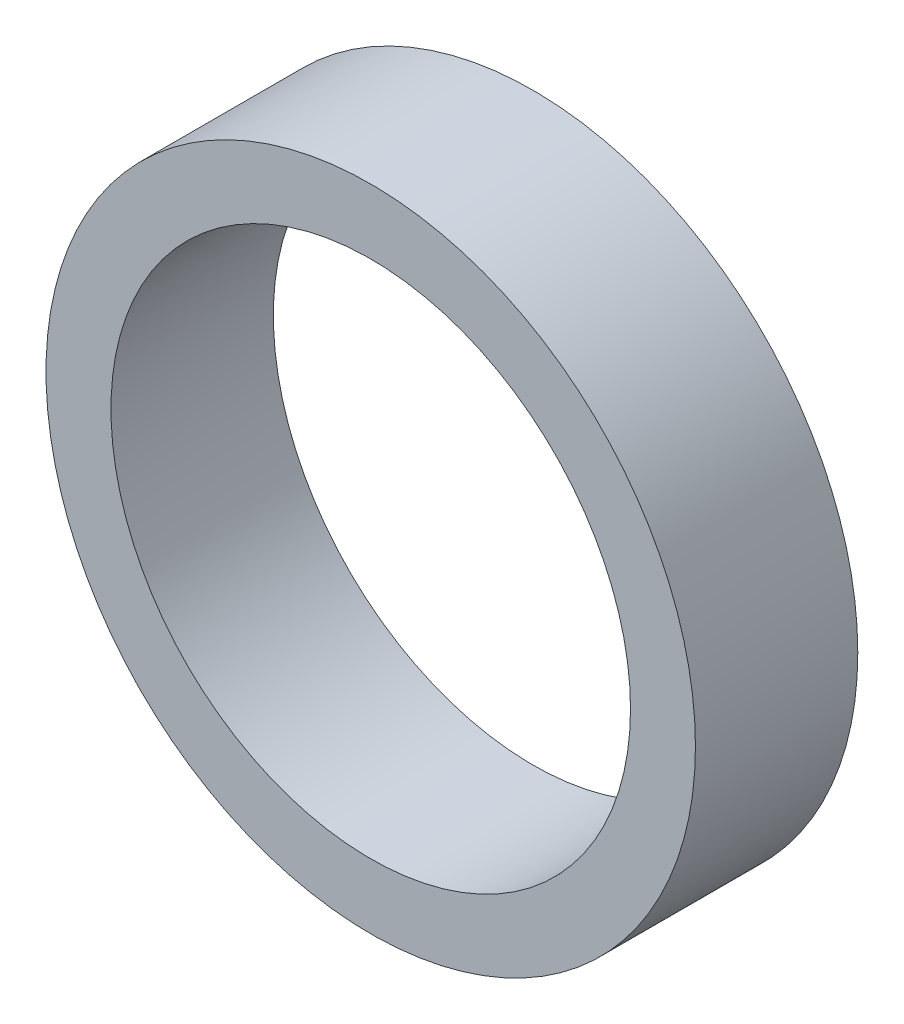
SolidWorks part; units mm, degrees
ref_plane "Front Plane" through (0, 0, 0) normal (0, 0, 1) x (1, 0, 0)
ref_plane "Top Plane" through (0, 0, 0) normal (0, 1, 0) x (1, 0, 0)
ref_plane "Right Plane" through (0, 0, 0) normal (1, 0, 0) x (0, 0, -1)
sketch "Sketch1" plane through (0, 0, 0) normal (0, 0, 1) x (1, 0, 0)
  circle A0 centre (0, 0) radius 20
  dimension "D1" = 40
extrude "Boss-Extrude1" add sketch "Sketch1" along normal blind 10
sketch "Sketch2" plane through (0, 0, 10) normal (0, 0, 1) x (1, 0, 0)
  circle A0 centre (0, 0) radius 16
  dimension "D1" = 32
extrude "Cut-Extrude1" cut sketch "Sketch2" against normal through all
